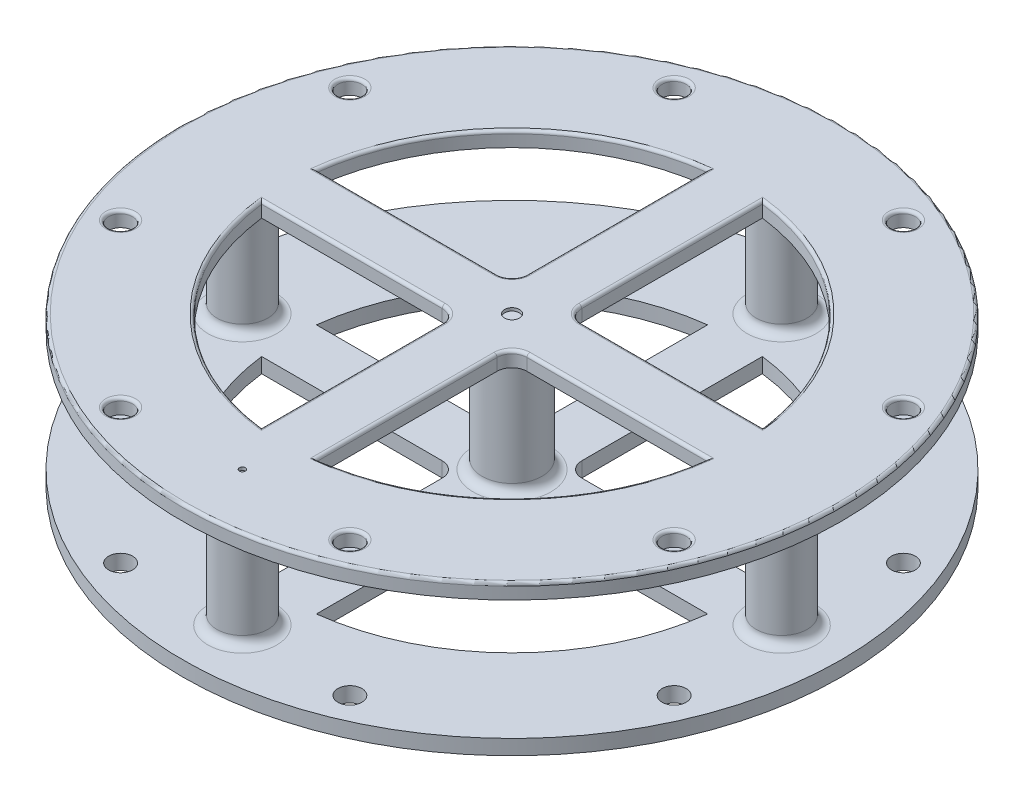
SolidWorks part; units mm, degrees
ref_plane "Front Plane" through (0, 0, 0) normal (0, 0, 1) x (1, 0, 0)
ref_plane "Top Plane" through (0, 0, 0) normal (0, 1, 0) x (1, 0, 0)
ref_plane "Right Plane" through (0, 0, 0) normal (1, 0, 0) x (0, 0, -1)
sketch "Sketch1" plane through (0, 0, 0) normal (0, 1, 0) x (1, 0, 0)
  line L0 (0, 0) -> (0, -279.4) construction
  line L5 (-35.921, -23.221) -> (-189.0794, -23.221)
  line L6 (-23.221, -35.921) -> (-23.221, -189.0794)
  line L7 (0, 0) -> (-279.4, 0) construction
  line L8 (0, 0) -> (-197.5656, -197.5656) construction
  line L9 (0, 0) -> (-106.9218, -258.1319) construction
  line L10 (0, 0) -> (-258.1319, -106.9218) construction
  line L11 (-23.221, 35.921) -> (-23.221, 189.0794)
  line L12 (-35.921, 23.221) -> (-189.0794, 23.221)
  line L13 (35.921, 23.221) -> (189.0794, 23.221)
  line L14 (23.221, 35.921) -> (23.221, 189.0794)
  line L15 (23.221, -35.921) -> (23.221, -189.0794)
  line L16 (35.921, -23.221) -> (189.0794, -23.221)
  circle A0 centre (0, 0) radius 228.6
  circle A1 centre (0, 0) radius 279.4
  circle A2 centre (0, 0) radius 254 construction
  circle A3 centre (-234.6654, -97.2016) radius 10.16
  circle A4 centre (-97.2016, -234.6654) radius 10.16
  circle A5 centre (0, 0) radius 254 construction
  circle A6 centre (-97.2016, 234.6654) radius 10.16
  circle A7 centre (-234.6654, 97.2016) radius 10.16
  circle A8 centre (0, 0) radius 254 construction
  circle A9 centre (234.6654, 97.2016) radius 10.16
  circle A10 centre (97.2016, 234.6654) radius 10.16
  circle A11 centre (0, 0) radius 254 construction
  circle A12 centre (97.2016, -234.6654) radius 10.16
  circle A13 centre (234.6654, -97.2016) radius 10.16
  arc A14 (23.221, -189.0794) -> (189.0794, -23.221) centre (0, 0) ccw
  circle A15 centre (0, 0) radius 50.8 construction
  arc A16 (-23.221, -35.921) -> (-35.921, -23.221) centre (-35.921, -35.921) ccw
  arc A17 (-35.921, 23.221) -> (-23.221, 35.921) centre (-35.921, 35.921) ccw
  arc A18 (23.221, 35.921) -> (35.921, 23.221) centre (35.921, 35.921) ccw
  arc A19 (35.921, -23.221) -> (23.221, -35.921) centre (35.921, -35.921) ccw
  arc A20 (-189.0794, -23.221) -> (-23.221, -189.0794) centre (0, 0) ccw
  arc A21 (189.0794, 23.221) -> (23.221, 189.0794) centre (0, 0) ccw
  arc A22 (-23.221, 189.0794) -> (-189.0794, 23.221) centre (0, 0) ccw
  point P33 (0, 0)
  point P56 (0, 0)
  dimension "D1" = 457.2
  dimension "D6" = 508
  dimension "D7" = 20.32
  dimension "D8" = 20.32
  dimension "D10" = 381
  dimension "D11" = 101.6
  dimension "D12" = 25.4
  dimension "D3" = 22.5
  dimension "D4" = 22.5
  dimension "D5" = 45
  dimension "D2" = 50.8
  dimension "D9" = 4
  dimension "D13" = 4
extrude "Boss-Extrude1" add sketch "Sketch1" along normal blind 127 contours A0 A22 L11 A17 L12 A21 L13 A18 L14 A20 L5 A16 L6 A19 L16 A14 L15 | A1 A13 A12 A10 A9 A7 A6 A4 A3 A0
fillet "Fillet1" radius 2.54 25 edges at (0, 127, 279.4) (-234.6654, 127, 107.3616) (-97.2016, 127, 244.8254) (-97.2016, 127, -224.5054) (-234.6654, 127, -87.0416) (234.6654, 127, -87.0416) (97.2016, 127, -224.5054) (97.2016, 127, 244.8254) (234.6654, 127, 107.3616) (23.221, 127, 112.5002) (134.7038, 127, 134.7038) (112.5002, 127, 23.221) (26.9408, 127, 26.9408) (-23.221, 127, 112.5002) (-26.9408, 127, 26.9408) (-112.5002, 127, 23.221) (-134.7038, 127, 134.7038) (23.221, 127, -112.5002) (26.9408, 127, -26.9408) (112.5002, 127, -23.221) (134.7038, 127, -134.7038) (-112.5002, 127, -23.221) (-26.9408, 127, -26.9408) (-23.221, 127, -112.5002) (-134.7038, 127, -134.7038)
sketch "Sketch2" plane through (0, 0, 0) normal (0, 0, 1) x (1, 0, 0)
  line L0 (-279.4, 124.46) -> (-279.4, 0) construction
  line L1 (-279.4, 114.3) -> (279.4, 114.3)
  line L2 (-279.4, 114.3) -> (-279.4, 12.7)
  line L3 (-279.4, 12.7) -> (279.4, 12.7)
  line L4 (279.4, 114.3) -> (279.4, 12.7)
  line L5 (279.4, 0) -> (279.4, 124.46) construction
  dimension "D1" = 101.6
  dimension "D2" = 12.7
extrude "Cut-Extrude1" cut sketch "Sketch2" against normal through all both and the other way through all
sketch "Sketch3" plane through (0, 0, 0) normal (0, -1, 0) x (1, 0, 0)
  circle A0 centre (0, 0) radius 6.35
  dimension "D1" = 12.7
extrude "Cut-Extrude2" cut sketch "Sketch3" against normal blind 6.35
sketch "Sketch5" plane through (0, 0, 0) normal (0, -1, 0) x (1, 0, 0)
  line L0 (0, 0) -> (0, 190.5) construction
  circle A0 centre (0, 0) radius 190.5 construction
  circle A1 centre (0, 190.5) radius 3.175
  circle A2 centre (0, 0) radius 190.5 construction
  circle A3 centre (190.5, 0) radius 3.175
  circle A4 centre (0, 0) radius 190.5 construction
  circle A5 centre (0, -190.5) radius 3.175
  circle A6 centre (0, 0) radius 190.5 construction
  circle A7 centre (-190.5, 0) radius 3.175
  point P17 (0, 0)
  dimension "D1" = 381
  dimension "D2" = 6.35
  dimension "D3" = 4
extrude "Boss-Extrude3" add sketch "Sketch5" along normal blind 2.54
sketch "Sketch6" plane through (0, 114.3, 0) normal (0, -1, 0) x (1, 0, 0)
  line L0 (0, 0) -> (0, 228.6) construction
  circle A0 centre (0, 0) radius 25.4
  circle A1 centre (0, 0) radius 228.6 construction
  circle A2 centre (0, 228.6) radius 21.59
  circle A3 centre (0, 0) radius 228.6 construction
  circle A4 centre (228.6, 0) radius 21.59
  circle A5 centre (0, 0) radius 228.6 construction
  circle A6 centre (0, -228.6) radius 21.59
  circle A7 centre (0, 0) radius 228.6 construction
  circle A8 centre (-228.6, 0) radius 21.59
  point P18 (0, 0)
  dimension "D1" = 50.8
  dimension "D2" = 457.2
  dimension "D3" = 43.18
  dimension "D4" = 4
extrude "Boss-Extrude4" add sketch "Sketch6" along normal up to next
fillet "Fillet2" radius 7.62 2 edges at (25.4, 12.7, 0) (-25.4, 114.3, 0)
fillet "Fillet3" radius 7.62 8 edges at (250.19, 12.7, 0) (207.01, 114.3, 0) (21.59, 12.7, 228.6) (-21.59, 114.3, 228.6) (21.59, 12.7, -228.6) (-21.59, 114.3, -228.6) (-207.01, 12.7, 0) (-250.19, 114.3, 0)
sketch "Sketch7" plane through (0, 127, 0) normal (0, 1, 0) x (1, 0, 0)
  line L0 (0, 0) -> (0, -228.6) construction
  circle A0 centre (0, 0) radius 6.35
  circle A2 centre (0, 0) radius 228.6 construction
  circle A3 centre (0, -228.6) radius 2.54
  dimension "D1" = 12.7
  dimension "D2" = 457.2
  dimension "D3" = 5.08
extrude "Cut-Extrude3" cut sketch "Sketch7" against normal blind 2.54
